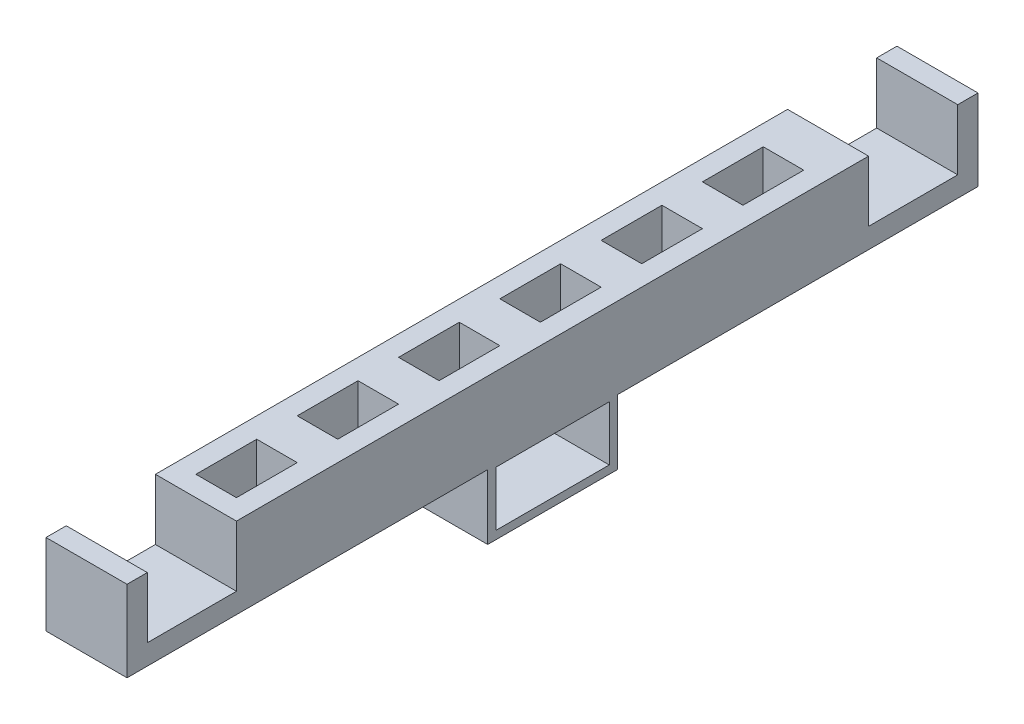
SolidWorks part; units mm, degrees
ref_plane "Front Plane" through (0, 0, 0) normal (0, 0, 1) x (1, 0, 0)
ref_plane "Top Plane" through (0, 0, 0) normal (0, 1, 0) x (1, 0, 0)
ref_plane "Right Plane" through (0, 0, 0) normal (1, 0, 0) x (0, 0, -1)
sketch "Sketch1" plane through (0, 0, 0) normal (0, 1, 0) x (1, 0, 0)
  line L1 (0, 0) -> (20, 0)
  line L2 (0, 0) -> (0, 210)
  line L3 (0, 210) -> (20, 210)
  line L4 (20, 0) -> (20, 210)
  dimension "D1" = 210
  dimension "20" = 20
extrude "Boss-Extrude1" add sketch "Sketch1" along normal blind 20
sketch "Sketch2" plane through (0, 20, 0) normal (0, 1, 0) x (1, 0, 0)
  line L0 (20, 0) -> (20, 210) construction
  line L1 (0, 5) -> (20, 5)
  line L2 (0, 5) -> (0, 27)
  line L3 (0, 27) -> (20, 27)
  line L4 (20, 5) -> (20, 27)
  line L5 (0, 0) -> (20, 0) construction
  dimension "D1" = 22
  dimension "D2" = 20
  dimension "D3" = 5
extrude "Cut-Extrude1" cut sketch "Sketch2" against normal blind 15
sketch "Sketch3" plane through (0, 20, 0) normal (0, 1, 0) x (1, 0, 0)
  line L0 (0, 210) -> (20, 210) construction
  line L1 (0, 205) -> (20, 205)
  line L2 (0, 205) -> (0, 183)
  line L3 (0, 183) -> (20, 183)
  line L4 (20, 205) -> (20, 183)
  line L5 (0, 0) -> (0, 210) construction
  dimension "D1" = 20
  dimension "D2" = 22
  dimension "D3" = 5
extrude "Cut-Extrude2" cut sketch "Sketch3" against normal blind 15
sketch "Sketch4" plane through (0, 20, 0) normal (0, 1, 0) x (1, 0, 0)
  line L0 (20, 0) -> (20, 210) construction
  line L1 (5, 32) -> (15, 32)
  line L2 (5, 32) -> (5, 47)
  line L3 (5, 47) -> (15, 47)
  line L4 (15, 32) -> (15, 47)
  line L5 (20, 27) -> (0, 27) construction
  line L6 (5, 57) -> (5, 72)
  line L7 (5, 57) -> (15, 57)
  line L8 (15, 57) -> (15, 72)
  line L9 (5, 72) -> (15, 72)
  line L10 (5, 82) -> (5, 97)
  line L11 (5, 82) -> (15, 82)
  line L12 (15, 82) -> (15, 97)
  line L13 (5, 97) -> (15, 97)
  line L14 (5, 107) -> (5, 122)
  line L15 (5, 107) -> (15, 107)
  line L16 (15, 107) -> (15, 122)
  line L17 (5, 122) -> (15, 122)
  line L18 (5, 132) -> (5, 147)
  line L19 (5, 132) -> (15, 132)
  line L20 (15, 132) -> (15, 147)
  line L21 (5, 147) -> (15, 147)
  line L22 (5, 157) -> (5, 172)
  line L23 (5, 157) -> (15, 157)
  line L24 (15, 157) -> (15, 172)
  line L25 (5, 172) -> (15, 172)
  dimension "D1" = 5
  dimension "D2" = 10
  dimension "D3" = 15
  dimension "D4" = 5
  dimension "D5" = 6
extrude "Cut-Extrude3" cut sketch "Sketch4" against normal through all
sketch "Sketch5" plane through (0, 0, 0) normal (0, -1, 0) x (-1, 0, 0)
  line L0 (23.7342, 105) -> (-57.5947, 105) construction
  line L1 (0, 0) -> (-20, 0) construction
  line L2 (0, 0) -> (0, 210) construction
  line L3 (0, 89) -> (-20, 89)
  line L4 (0, 89) -> (0, 121)
  line L5 (0, 121) -> (-20, 121)
  line L6 (-20, 89) -> (-20, 121)
  line L7 (-20, 0) -> (-20, 210) construction
  dimension "D1" = 105
  dimension "D2" = 32
  dimension "D3" = 16
extrude "Boss-Extrude2" add sketch "Sketch5" along normal blind 16
sketch "Sketch6" plane through (20, 0, 0) normal (1, 0, 0) x (0, 0, -1)
  line L0 (121, -16) -> (121, 0) construction
  line L1 (91, -14) -> (119, -14)
  line L2 (91, -14) -> (91, -0.5)
  line L3 (91, -0.5) -> (119, -0.5)
  line L4 (119, -14) -> (119, -0.5)
  line L5 (121, -16) -> (89, -16) construction
  dimension "D1" = 28
  dimension "D2" = 2
  dimension "D3" = 13.5
  dimension "D4" = 2
extrude "Cut-Extrude4" cut sketch "Sketch6" against normal through all
